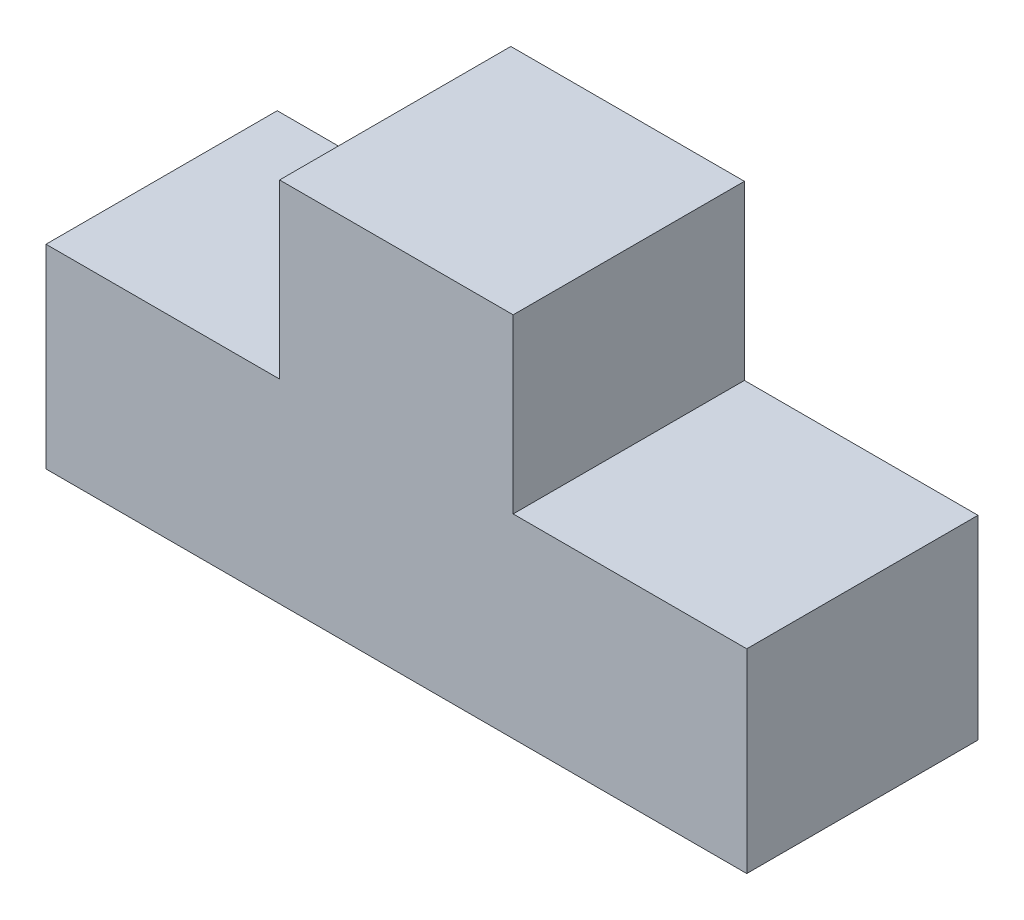
SolidWorks part; units mm, degrees
ref_plane "Front Plane" through (0, 0, 0) normal (0, 0, 1) x (1, 0, 0)
ref_plane "Top Plane" through (0, 0, 0) normal (0, 1, 0) x (1, 0, 0)
ref_plane "Right Plane" through (0, 0, 0) normal (1, 0, 0) x (0, 0, -1)
sketch "Sketch1" plane through (0, 0, 0) normal (0, 0, 1) x (1, 0, 0)
  line L0 (0, 0) -> (2286, 0)
  line L1 (2286, 0) -> (2286, 635)
  line L2 (2286, 635) -> (1524, 635)
  line L3 (1524, 635) -> (1524, 1197.5857)
  line L4 (1524, 1197.5857) -> (762, 1197.5857)
  line L5 (762, 1197.5857) -> (762, 635)
  line L6 (762, 635) -> (0, 635)
  line L7 (0, 635) -> (0, 0)
  dimension "D1" = 2286
  dimension "D2" = 635
  dimension "D3" = 762
  dimension "D4" = 762
  dimension "D5" = 635
extrude "Boss-Extrude1" add sketch "Sketch1" along normal blind 754.38 contours L0 L1 L2 L3 L4 L5 L6 L7
